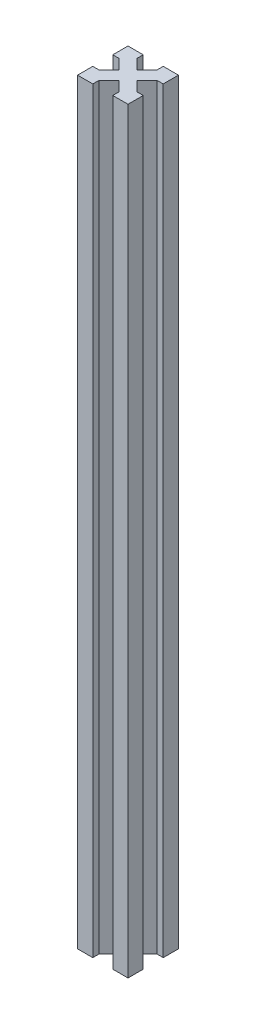
SolidWorks part; units mm, degrees
ref_plane "Plan de face" through (0, 0, 0) normal (0, 0, 1) x (1, 0, 0)
ref_plane "Plan de dessus" through (0, 0, 0) normal (0, 1, 0) x (1, 0, 0)
ref_plane "Plan de droite" through (0, 0, 0) normal (1, 0, 0) x (0, 0, -1)
sketch "Esquisse1" plane through (0, 0, 0) normal (0, 1, 0) x (1, 0, 0)
  line L0 (-2.5, 17.5) -> (-17.5, 17.5)
  line L1 (0, 0) -> (-20, 0)
  line L2 (0, 0) -> (0, 20)
  line L3 (0, 20) -> (-20, 20)
  line L4 (-20, 0) -> (-20, 20)
  line L5 (0, 20) -> (-20, 0) construction
  line L6 (-17.5, 2.5) -> (-17.5, 17.5)
  line L11 (-2.5, 2.5) -> (-17.5, 2.5)
  line L12 (-2.5, 2.5) -> (-2.5, 17.5)
  line L13 (-20, 20) -> (0, 0) construction
  line L14 (-26.9957, 23.4601) -> (-23.4601, 26.9957)
  line L15 (-26.9957, 23.4601) -> (3.4601, -6.9957)
  line L16 (-23.4601, 26.9957) -> (6.9957, -3.4601)
  line L17 (3.4601, -6.9957) -> (6.9957, -3.4601)
  line L18 (-26.9957, 23.4601) -> (6.9957, -3.4601) construction
  line L19 (-23.4601, 26.9957) -> (3.4601, -6.9957) construction
  line L20 (-10, 20) -> (-10, 0) construction
  line L21 (-23.4601, -6.9957) -> (-26.9957, -3.4601)
  line L22 (3.4601, 26.9957) -> (-26.9957, -3.4601)
  line L23 (6.9957, 23.4601) -> (-23.4601, -6.9957)
  line L24 (6.9957, 23.4601) -> (3.4601, 26.9957)
  line L25 (-17.5, 13.9645) -> (-20, 13.9645)
  line L26 (-20, 10) -> (0, 10) construction
  line L27 (-17.5, 6.0355) -> (-20, 6.0355)
  line L28 (-2.5, 6.0355) -> (0, 6.0355)
  line L29 (-2.5, 13.9645) -> (0, 13.9645)
  line L30 (-2.5, 6.0355) -> (0, 6.0355)
  line L31 (-2.5, 13.9645) -> (0, 13.9645)
  line L32 (-13.9645, 2.5) -> (-13.9645, 0)
  line L33 (-6.0355, 17.5) -> (-6.0355, 20)
  line L34 (-13.9645, 17.5) -> (-13.9645, 20)
  line L35 (-6.0355, 2.5) -> (-6.0355, 0)
  point P11 (-10, 10)
  dimension "D1" = 20
  dimension "D2" = 20
  dimension "D3" = 7.3934
  dimension "D4" = 2.5
  dimension "D5" = 43.071
  dimension "D6" = 2.5
extrude "Boss.-Extru.1" add sketch "Esquisse1" along normal blind 300 contours L15 L35 L1 | L16 L12 L11 L15 L1 L2 | L28 L16 L2 | L16 L23 L15 L11 L12 | L32 L23 L1 | L23 L11 L6 L22 L4 L1 | L22 L27 L4 | L23 L15 L22 L6 L11 | L23 L16 L22 L15 | L23 L12 L0 L22 L16 | L23 L2 L3 L22 L0 L12 | L23 L29 L2 | L33 L22 L3 | L16 L34 L3 | L16 L3 L4 L15 L6 L0 | L25 L15 L4 | L22 L16 L0 L6 L15
